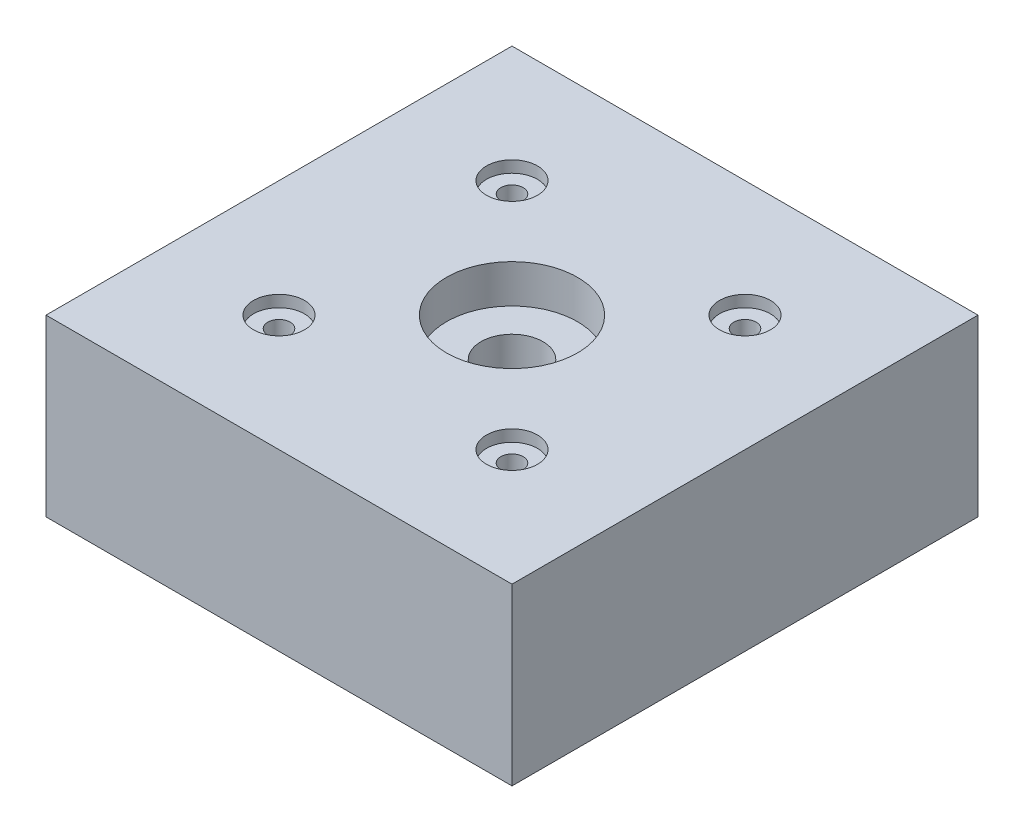
SolidWorks part; units mm, degrees
ref_plane "Front Plane" through (0, 0, 0) normal (0, 0, 1) x (1, 0, 0)
ref_plane "Top Plane" through (0, 0, 0) normal (0, 1, 0) x (1, 0, 0)
ref_plane "Right Plane" through (0, 0, 0) normal (1, 0, 0) x (0, 0, -1)
sketch "Sketch1" plane through (0, 0, 0) normal (0, 1, 0) x (1, 0, 0)
  line L1 (25.4, -25.4) -> (-25.4, -25.4)
  line L2 (25.4, -25.4) -> (25.4, 25.4)
  line L3 (25.4, 25.4) -> (-25.4, 25.4)
  line L4 (-25.4, -25.4) -> (-25.4, 25.4)
  line L5 (25.4, -25.4) -> (-25.4, 25.4) construction
  line L6 (25.4, 25.4) -> (-25.4, -25.4) construction
  point P0 (0, 0)
  dimension "D1" = 50.8
extrude "Boss-Extrude1" add sketch "Sketch1" along normal blind 19.05
hole_wizard "CBORE for 1/4 Binding Head Machine Screw1" positions "Sketch2" profile "Sketch3" counterbore size "1/4" standard "ANSI Inch" end condition through all
sketch "Sketch2" plane through (0, 19.05, 0) normal (0, 1, 0) x (1, 0, 0)
  point P0 (0, 0)
sketch "Sketch3" plane through (0, 19.05, 0) normal (1, 0, 0) x (0, 0, 1)
  line L0 (0, 0) -> (0, 19.05)
  line L1 (0, 19.05) -> (3.3782, 19.05)
  line L2 (3.3782, 19.05) -> (3.3782, 4.191)
  line L3 (3.3782, 4.191) -> (7.1437, 4.191)
  line L4 (7.1437, 4.191) -> (7.1437, 0)
  line L5 (7.1437, 0) -> (0, 0)
  line L6 (0, -6.35) -> (0, 107.95) construction
  dimension "Thru Hole Dia." = 6.7564
  dimension "Thru Hole Depth" = 19.05
  dimension "C'Bore Dia." = 14.2875
  dimension "C'Bore Depth" = 4.191
hole_wizard "CBORE for #2 Binding Head Machine Screw1" positions "Sketch4" profile "Sketch5" counterbore size "#2" standard "ANSI Inch" end condition through all
sketch "Sketch4" plane through (0, 19.05, 0) normal (0, 1, 0) x (1, 0, 0)
  line L1 (12.7, -12.7) -> (-12.7, -12.7)
  line L2 (12.7, -12.7) -> (12.7, 12.7)
  line L3 (12.7, 12.7) -> (-12.7, 12.7)
  line L4 (-12.7, -12.7) -> (-12.7, 12.7)
  line L5 (12.7, -12.7) -> (-12.7, 12.7) construction
  line L6 (12.7, 12.7) -> (-12.7, -12.7) construction
  point P0 (-12.7, 12.7)
  point P3 (0, 0)
sketch "Sketch5" plane through (-12.7, 19.05, -12.7) normal (1, 0, 0) x (0, 0, 1)
  line L0 (0, 0) -> (0, 19.05)
  line L1 (0, 19.05) -> (1.2192, 19.05)
  line L2 (1.2192, 19.05) -> (1.2192, 1.27)
  line L3 (1.2192, 1.27) -> (2.7788, 1.27)
  line L4 (2.7788, 1.27) -> (2.7788, 0)
  line L5 (2.7788, 0) -> (0, 0)
  line L6 (0, -6.35) -> (0, 107.95) construction
  dimension "Thru Hole Dia." = 2.4384
  dimension "Thru Hole Depth" = 19.05
  dimension "C'Bore Dia." = 5.5575
  dimension "C'Bore Depth" = 1.27
hole_wizard "CBORE for #2 Binding Head Machine Screw2" positions "Sketch6" profile "Sketch7" counterbore size "#2" standard "ANSI Inch" end condition through all
sketch "Sketch6" plane through (0, 19.05, 0) normal (0, 1, 0) x (1, 0, 0)
  point P0 (12.7, 12.7)
  point P1 (-12.7, -12.7)
  point P2 (12.7, -12.7)
sketch "Sketch7" plane through (12.7, 19.05, -12.7) normal (1, 0, 0) x (0, 0, 1)
  line L0 (0, 0) -> (0, 19.05)
  line L1 (0, 19.05) -> (1.2192, 19.05)
  line L2 (1.2192, 19.05) -> (1.2192, 1.27)
  line L3 (1.2192, 1.27) -> (2.7788, 1.27)
  line L4 (2.7788, 1.27) -> (2.7788, 0)
  line L5 (2.7788, 0) -> (0, 0)
  line L6 (0, -6.35) -> (0, 107.95) construction
  dimension "Thru Hole Dia." = 2.4384
  dimension "Thru Hole Depth" = 19.05
  dimension "C'Bore Dia." = 5.5575
  dimension "C'Bore Depth" = 1.27
equation "\".hf\"=0.1"
